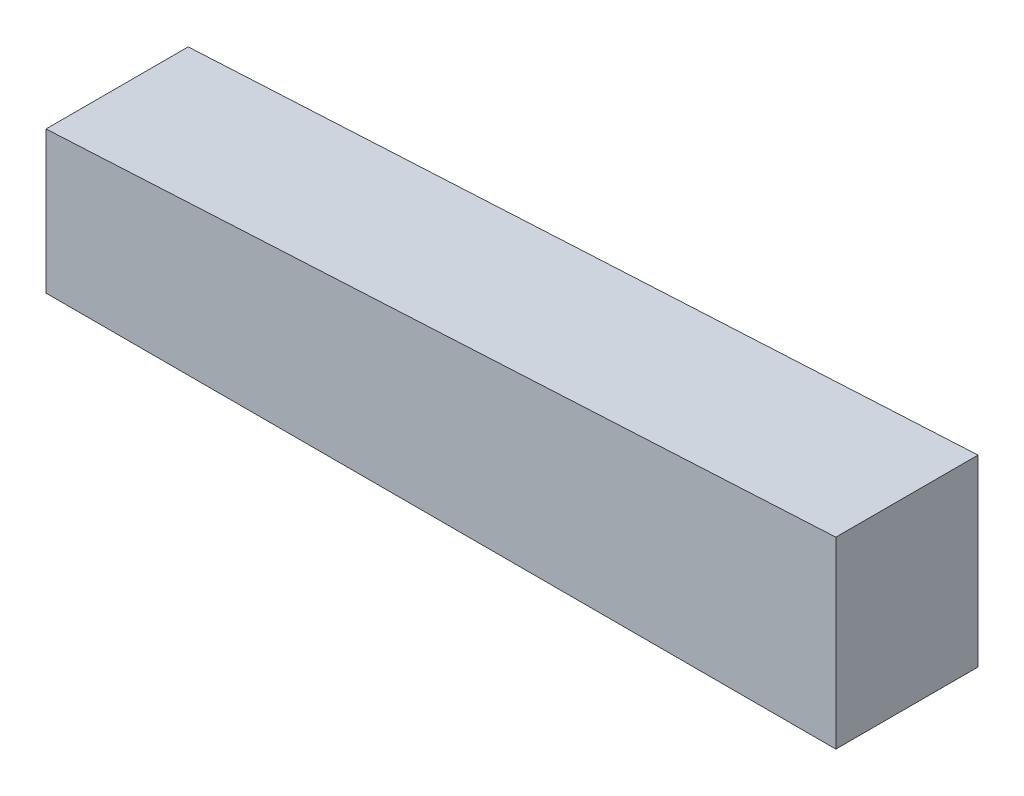
SolidWorks part; units mm, degrees
ref_plane "Front Plane" through (0, 0, 0) normal (0, 0, 1) x (1, 0, 0)
ref_plane "Top Plane" through (0, 0, 0) normal (0, 1, 0) x (1, 0, 0)
ref_plane "Right Plane" through (0, 0, 0) normal (1, 0, 0) x (0, 0, -1)
sketch "Sketch1" plane through (0, 0, 0) normal (0, 0, 1) x (1, 0, 0)
  line L0 (0, 0) -> (25, 0)
  line L1 (25, 0) -> (25, 5.8102)
  line L2 (0, 0) -> (0, 4.5)
  line L3 (0, 4.5) -> (25, 5.8102)
  dimension "D1" = 25
  dimension "D2" = 4.5
  dimension "D3" = 3
extrude "Boss-Extrude1" add sketch "Sketch1" along normal blind 4.5
